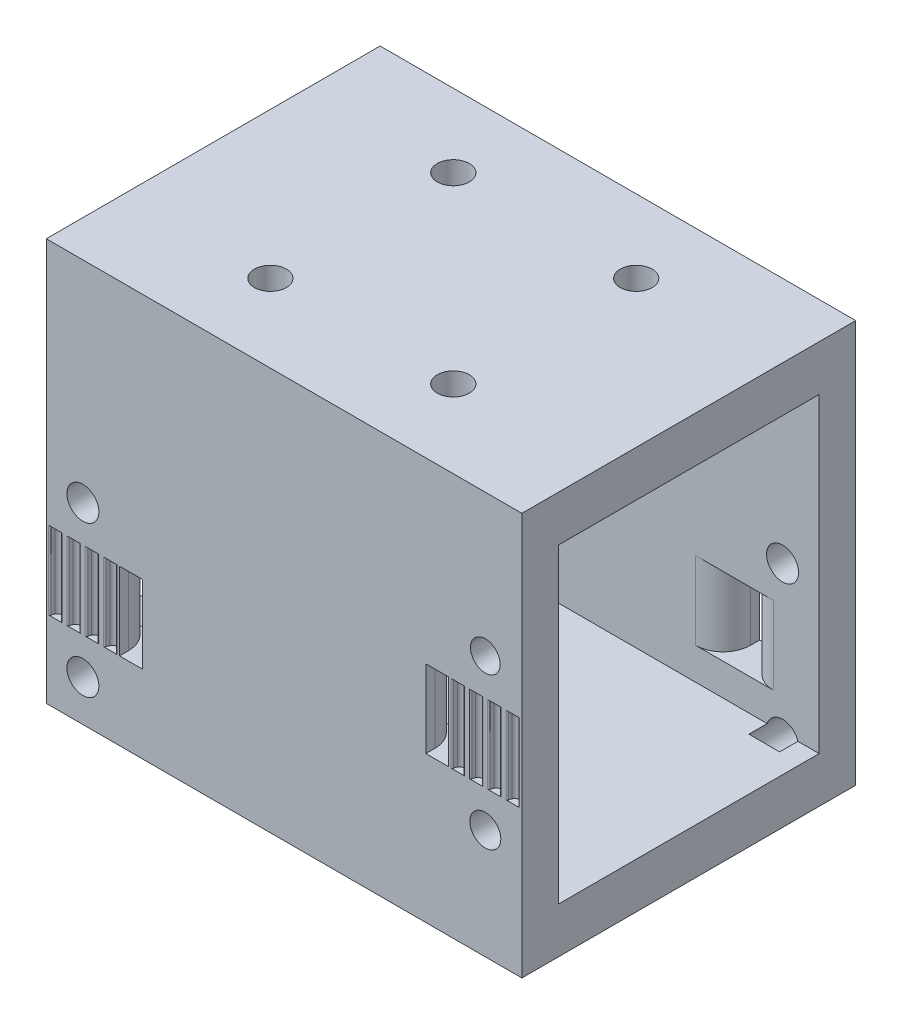
SolidWorks part; units mm, degrees
ref_plane "Front Plane" through (0, 0, 0) normal (0, 0, 1) x (1, 0, 0)
ref_plane "Top Plane" through (0, 0, 0) normal (0, 1, 0) x (1, 0, 0)
ref_plane "Right Plane" through (0, 0, 0) normal (1, 0, 0) x (0, 0, -1)
sketch "Sketch1" plane through (0, 0, 0) normal (0, 1, 0) x (1, 0, 0)
  line L1 (-17.9365, 20.045) -> (34.0635, 20.045)
  line L2 (-17.9365, 20.045) -> (-17.9365, -16.455)
  line L3 (-17.9365, -16.455) -> (34.0635, -16.455)
  line L4 (34.0635, 20.045) -> (34.0635, -16.455)
  circle A0 centre (-1.9365, 12.045) radius 1.75
  circle A1 centre (18.0635, 12.045) radius 1.75
  circle A2 centre (18.0635, -7.955) radius 1.75
  circle A3 centre (-1.9365, -7.955) radius 1.75
  dimension "D1" = 20
  dimension "D2" = 20
  dimension "D3" = 20
  dimension "D4" = 20
  dimension "D5" = 3.5
  dimension "D6" = 3.5
  dimension "D7" = 3.5
  dimension "D8" = 3.5
  dimension "D10" = 16
  dimension "D12" = 8.5
  dimension "D13" = 16
  dimension "D9" = 16
  dimension "D11" = 8
extrude "Boss-Extrude1" add sketch "Sketch1" along normal blind 5
sketch "Sketch2" plane through (0, 0, 0) normal (0, -1, 0) x (1, 0, 0)
  line L0 (34.0635, 16.455) -> (34.0635, -20.045) construction
  line L1 (-17.9365, 16.455) -> (34.0635, 16.455)
  line L2 (-17.9365, 16.455) -> (-17.9365, 12.455)
  line L3 (-17.9365, 12.455) -> (34.0635, 12.455)
  line L4 (34.0635, 16.455) -> (34.0635, 12.455)
  line L6 (-17.9365, -20.045) -> (34.0635, -20.045)
  line L7 (-17.9365, -20.045) -> (-17.9365, -16.045)
  line L8 (-17.9365, -16.045) -> (34.0635, -16.045)
  line L9 (34.0635, -20.045) -> (34.0635, -16.045)
  dimension "D1" = 4
  dimension "D2" = 4
extrude "Boss-Extrude2" add sketch "Sketch2" along normal blind 34
sketch "Sketch3" plane through (0, -34, 0) normal (0, -1, 0) x (1, 0, 0)
  line L1 (-17.9365, 16.455) -> (34.0635, 16.455)
  line L2 (-17.9365, 16.455) -> (-17.9365, -20.045)
  line L3 (-17.9365, -20.045) -> (34.0635, -20.045)
  line L4 (34.0635, 16.455) -> (34.0635, -20.045)
extrude "Boss-Extrude3" add sketch "Sketch3" along normal blind 5
sketch "Sketch4" plane through (0, 0, 16.455) normal (0, 0, 1) x (1, 0, 0)
  line L0 (-17.9365, 5) -> (-17.9365, -39) construction
  line L1 (26.0635, -14.5) -> (23.5635, -14.5)
  line L2 (26.0635, -14.5) -> (26.0635, -23)
  line L3 (26.0635, -23) -> (23.5635, -23)
  line L4 (23.5635, -14.5) -> (23.5635, -23)
  line L5 (-9.9365, -22) -> (-7.4365, -22)
  line L6 (-9.9365, -22) -> (-9.9365, -30.5)
  line L7 (-9.9365, -30.5) -> (-7.4365, -30.5)
  line L8 (-7.4365, -22) -> (-7.4365, -30.5)
  line L9 (34.0635, 5) -> (34.0635, -39) construction
  line L10 (34.0635, -39) -> (-17.9365, -39) construction
  line L11 (-17.9365, 5) -> (34.0635, 5) construction
  dimension "D1" = 2.5
  dimension "D2" = 8.5
  dimension "D3" = 8.5
  dimension "D4" = 2.5
  dimension "D5" = 8
  dimension "D6" = 8
  dimension "D7" = 8.5
  dimension "D8" = 19.5
extrude "Cut-Extrude1" cut sketch "Sketch4" against normal blind 8
ref_plane "Plane1" through (0, -30.5, 0) normal (0, 1, 0) x (1, 0, 0)
sketch "Sketch5" plane through (0, -30.5, 0) normal (0, 1, 0) x (1, 0, 0)
  line L4 (-9.9365, -12.455) -> (-9.9365, -16.455) construction
  line L6 (-9.9365, -16.455) -> (-7.4365, -16.455) construction
  line B0 (-9.9365, -17.085) -> (-13.9365, -17.085)
  line B1 (-11.6767, -16.455) -> (-12.1963, -16.455)
  line B2 (-12.9365, -15.705) -> (-12.9365, -17.2218) construction
  line B3 (-13.9365, -16.455) -> (-13.6767, -16.455)
  line B4 (-9.8127, -16.709) -> (-14.1468, -16.709) construction
  line B5 (-13.3365, -16.26) -> (-13.3365, -16.6085) construction
  line B6 (-11.9365, -17.2218) -> (-11.9365, -15.5499) construction
  line B7 (-9.9365, -16.455) -> (-10.1963, -16.455)
  line B8 (-9.8127, -15.705) -> (-14.1468, -15.705) construction
  line B9 (-9.9365, -16.455) -> (-9.9365, -17.085)
  line B10 (-13.9365, -17.085) -> (-13.9365, -16.455)
  arc B11 (-12.4376, -16.0168) -> (-13.4354, -16.0168) centre (-12.9365, -16.26) ccw
  arc B12 (-12.3451, -16.3246) -> (-12.4376, -16.0168) centre (-13.3365, -16.455) ccw
  arc B13 (-12.3451, -16.3246) -> (-12.1963, -16.455) centre (-12.1963, -16.305) ccw
  arc B14 (-13.528, -16.3246) -> (-13.6767, -16.455) centre (-13.6767, -16.305) cw
  arc B15 (-13.528, -16.3246) -> (-13.4354, -16.0168) centre (-12.5365, -16.455) cw
  arc B16 (-11.528, -16.3246) -> (-11.6767, -16.455) centre (-11.6767, -16.305) cw
  arc B17 (-11.528, -16.3246) -> (-11.4354, -16.0168) centre (-10.5365, -16.455) cw
  arc B18 (-10.3451, -16.3246) -> (-10.1963, -16.455) centre (-10.1963, -16.305) ccw
  arc B19 (-10.3451, -16.3246) -> (-10.4376, -16.0168) centre (-11.3365, -16.455) ccw
  arc B20 (-11.4354, -16.0168) -> (-10.4376, -16.0168) centre (-10.9365, -16.26) cw
  line B21 (-13.9365, -17.085) -> (-17.9365, -17.085)
  line B22 (-15.6767, -16.455) -> (-16.1963, -16.455)
  line B23 (-16.9365, -15.705) -> (-16.9365, -17.2218) construction
  line B24 (-17.9365, -16.455) -> (-17.6767, -16.455)
  line B25 (-13.8127, -16.709) -> (-18.1468, -16.709) construction
  line B26 (-17.3365, -16.26) -> (-17.3365, -16.6085) construction
  line B27 (-15.9365, -17.2218) -> (-15.9365, -15.5499) construction
  line B28 (-13.9365, -16.455) -> (-14.1963, -16.455)
  line B29 (-13.8127, -15.705) -> (-18.1468, -15.705) construction
  line B30 (-13.9365, -16.455) -> (-13.9365, -17.085)
  line B31 (-17.9365, -17.085) -> (-17.9365, -16.455)
  arc B32 (-16.4376, -16.0168) -> (-17.4354, -16.0168) centre (-16.9365, -16.26) ccw
  arc B33 (-16.3451, -16.3246) -> (-16.4376, -16.0168) centre (-17.3365, -16.455) ccw
  arc B34 (-16.3451, -16.3246) -> (-16.1963, -16.455) centre (-16.1963, -16.305) ccw
  arc B35 (-17.528, -16.3246) -> (-17.6767, -16.455) centre (-17.6767, -16.305) cw
  arc B36 (-17.528, -16.3246) -> (-17.4354, -16.0168) centre (-16.5365, -16.455) cw
  arc B37 (-15.528, -16.3246) -> (-15.6767, -16.455) centre (-15.6767, -16.305) cw
  arc B38 (-15.528, -16.3246) -> (-15.4354, -16.0168) centre (-14.5365, -16.455) cw
  arc B39 (-14.3451, -16.3246) -> (-14.1963, -16.455) centre (-14.1963, -16.305) ccw
  arc B40 (-14.3451, -16.3246) -> (-14.4376, -16.0168) centre (-15.3365, -16.455) ccw
  arc B41 (-15.4354, -16.0168) -> (-14.4376, -16.0168) centre (-14.9365, -16.26) cw
  dimension "D3" = 2
  dimension "D1" = 0
  dimension "D2" = 0
sketch_block_instance "Block1-1"
sketch_block "Block1" parameters "D4"=0.555, "D5"=1, "D6"=0.15, "D1"=0.254, "D2"=0.4, "D3"=1, "D7"=1.38, "D8"=0.75
sketch_block_instance "Block1-2"
extrude "Cut-Extrude2" cut sketch "Sketch5" along normal up to surface (8.5 mm away) contours B20 B17 B16 B1 B13 B12 B11 B15 B14 B3 B10 B0 B9 B7 B18 B19 | B41 B38 B37 B22 B34 B33 B32 B36 B35 B24 B31 B21 B10 B28 B39 B40 up to face at (-8.6865, -22, 14.455)
sketch "Sketch6" plane through (0, -23, 0) normal (0, 1, 0) x (1, 0, 0)
  line L0 (23.5635, -16.455) -> (26.0635, -16.455) construction
  line L1 (26.0635, -12.455) -> (26.0635, -16.455) construction
  line B0 (30.0635, -16.455) -> (29.8037, -16.455)
  line B1 (26.0635, -17.085) -> (26.0635, -16.455)
  line B2 (26.0635, -16.455) -> (26.3233, -16.455)
  arc B3 (26.472, -16.3246) -> (26.3233, -16.455) centre (26.3233, -16.305) cw
  arc B4 (26.472, -16.3246) -> (26.5646, -16.0168) centre (27.4635, -16.455) cw
  arc B5 (27.5624, -16.0168) -> (26.5646, -16.0168) centre (27.0635, -16.26) ccw
  arc B6 (27.6549, -16.3246) -> (27.5624, -16.0168) centre (26.6635, -16.455) ccw
  arc B7 (27.6549, -16.3246) -> (27.8037, -16.455) centre (27.8037, -16.305) ccw
  line B8 (28.3233, -16.455) -> (27.8037, -16.455)
  arc B9 (28.472, -16.3246) -> (28.3233, -16.455) centre (28.3233, -16.305) cw
  arc B10 (28.472, -16.3246) -> (28.5646, -16.0168) centre (29.4635, -16.455) cw
  arc B11 (28.5646, -16.0168) -> (29.5624, -16.0168) centre (29.0635, -16.26) cw
  arc B12 (29.6549, -16.3246) -> (29.5624, -16.0168) centre (28.6635, -16.455) ccw
  arc B13 (29.6549, -16.3246) -> (29.8037, -16.455) centre (29.8037, -16.305) ccw
  line B14 (30.0635, -16.455) -> (30.0635, -17.085)
  line B15 (30.0635, -17.085) -> (26.0635, -17.085)
  line B16 (27.0635, -15.705) -> (27.0635, -17.2218) construction
  line B17 (30.1873, -16.709) -> (25.8532, -16.709) construction
  line B18 (26.6635, -16.26) -> (26.6635, -16.6085) construction
  line B19 (28.0635, -17.2218) -> (28.0635, -15.5499) construction
  line B20 (30.1873, -15.705) -> (25.8532, -15.705) construction
  line B21 (34.0635, -17.085) -> (30.0635, -17.085)
  line B22 (32.3233, -16.455) -> (31.8037, -16.455)
  line B23 (31.0635, -15.705) -> (31.0635, -17.2218) construction
  line B24 (30.0635, -16.455) -> (30.3233, -16.455)
  line B25 (34.1873, -16.709) -> (29.8532, -16.709) construction
  line B26 (30.6635, -16.26) -> (30.6635, -16.6085) construction
  line B27 (32.0635, -17.2218) -> (32.0635, -15.5499) construction
  line B28 (34.0635, -16.455) -> (33.8037, -16.455)
  line B29 (34.1873, -15.705) -> (29.8532, -15.705) construction
  line B30 (34.0635, -16.455) -> (34.0635, -17.085)
  line B31 (30.0635, -17.085) -> (30.0635, -16.455)
  arc B32 (31.5624, -16.0168) -> (30.5646, -16.0168) centre (31.0635, -16.26) ccw
  arc B33 (31.6549, -16.3246) -> (31.5624, -16.0168) centre (30.6635, -16.455) ccw
  arc B34 (31.6549, -16.3246) -> (31.8037, -16.455) centre (31.8037, -16.305) ccw
  arc B35 (30.472, -16.3246) -> (30.3233, -16.455) centre (30.3233, -16.305) cw
  arc B36 (30.472, -16.3246) -> (30.5646, -16.0168) centre (31.4635, -16.455) cw
  arc B37 (32.472, -16.3246) -> (32.3233, -16.455) centre (32.3233, -16.305) cw
  arc B38 (32.472, -16.3246) -> (32.5646, -16.0168) centre (33.4635, -16.455) cw
  arc B39 (33.6549, -16.3246) -> (33.8037, -16.455) centre (33.8037, -16.305) ccw
  arc B40 (33.6549, -16.3246) -> (33.5624, -16.0168) centre (32.6635, -16.455) ccw
  arc B41 (32.5646, -16.0168) -> (33.5624, -16.0168) centre (33.0635, -16.26) cw
  dimension "D1" = 0
  dimension "D2" = 0
sketch_block_instance "Block2-1"
sketch_block "Block2"
sketch_block_instance "Block1-3"
sketch_block_instance "Block1-4"
extrude "Cut-Extrude3" cut sketch "Sketch6" along normal up to surface (8.5 mm away) contours B11 B10 B9 B8 B7 B6 B5 B4 B3 B2 B1 B15 B14 B0 B13 B12 | B41 B38 B37 B22 B34 B33 B32 B36 B35 B24 B14 B21 B30 B28 B39 B40 up to face at (24.8135, -14.5, 14.455)
sketch "Sketch7" plane through (0, 0, 16.455) normal (0, 0, 1) x (1, 0, 0)
  line L0 (-7.4365, -22) -> (-9.9365, -22) construction
  line L1 (-9.9365, -30.5) -> (-7.4365, -30.5) construction
  line L2 (-17.9365, 5) -> (-17.9365, -39) construction
  line L3 (32.5646, -14.5) -> (33.5624, -14.5) construction
  line L4 (34.0635, 5) -> (34.0635, -39) construction
  circle A0 centre (-13.9365, -34.5) radius 1.75
  circle A1 centre (-13.9365, -18) radius 1.75
  circle A2 centre (30.0635, -10.5) radius 1.6235
  circle A3 centre (30.0635, -27) radius 1.6945
  dimension "D1" = 16.5
  dimension "D2" = 4
  dimension "D4" = 4
  dimension "D5" = 4
  dimension "D6" = 3.5
  dimension "D7" = 3.5
  dimension "D8" = 16.5
  dimension "D9" = 4
  dimension "D10" = 4
  dimension "D11" = 4
  dimension "D3" = 4
extrude "Cut-Extrude4" cut sketch "Sketch7" against normal blind 6
sketch "Sketch8" plane through (0, 0, -20.045) normal (0, 0, -1) x (-1, 0, 0)
  line L0 (17.9365, -39) -> (-34.0635, -39) construction
  line L1 (-26.0635, -30.5) -> (-23.5635, -30.5)
  line L2 (-26.0635, -30.5) -> (-26.0635, -22)
  line L3 (-26.0635, -22) -> (-23.5635, -22)
  line L4 (-23.5635, -30.5) -> (-23.5635, -22)
  line L5 (7.4365, -23) -> (9.9365, -23)
  line L6 (7.4365, -23) -> (7.4365, -14.5)
  line L7 (7.4365, -14.5) -> (9.9365, -14.5)
  line L8 (9.9365, -23) -> (9.9365, -14.5)
  line L9 (-34.0635, 5) -> (-34.0635, -39) construction
  line L10 (-34.0635, 5) -> (17.9365, 5) construction
  line L11 (17.9365, 5) -> (17.9365, -39) construction
  dimension "D1" = 2.5
  dimension "D2" = 2.5
  dimension "D3" = 8.5
  dimension "D4" = 8.5
  dimension "D5" = 8.5
  dimension "D6" = 8
  dimension "D7" = 19.5
  dimension "D8" = 8
extrude "Cut-Extrude5" cut sketch "Sketch8" against normal blind 6
fillet "Fillet1" radius 3 8 edges at (26.0635, -26.25, -16.045) (23.5635, -26.25, -16.045) (-7.4365, -18.75, -16.045) (-9.9365, -18.75, -16.045) (-9.9365, -26.25, 12.455) (-7.4365, -26.25, 12.455) (23.5635, -18.75, 12.455) (26.0635, -18.75, 12.455)
sketch "Sketch9" plane through (0, 0, -20.045) normal (0, 0, -1) x (-1, 0, 0)
  line L0 (9.9365, -14.5) -> (7.4365, -14.5) construction
  line L1 (17.9365, 5) -> (17.9365, -39) construction
  line L2 (-34.0635, 5) -> (-34.0635, -39) construction
  line L3 (-26.0635, -30.5) -> (-23.5635, -30.5) construction
  circle A0 centre (13.9365, -10.5) radius 1.75
  circle A1 centre (13.9365, -27) radius 1.75
  circle A2 centre (-30.0635, -18) radius 1.75
  circle A3 centre (-30.0635, -34.5) radius 1.75
  dimension "D1" = 16.5
  dimension "D3" = 4
  dimension "D4" = 4
  dimension "D5" = 3.5
  dimension "D6" = 3.5
  dimension "D7" = 16.5
  dimension "D8" = 4
  dimension "D9" = 4
  dimension "D10" = 4
  dimension "D11" = 3.5
  dimension "D12" = 3.5
  dimension "D2" = 4
extrude "Cut-Extrude6" cut sketch "Sketch9" against normal blind 6
